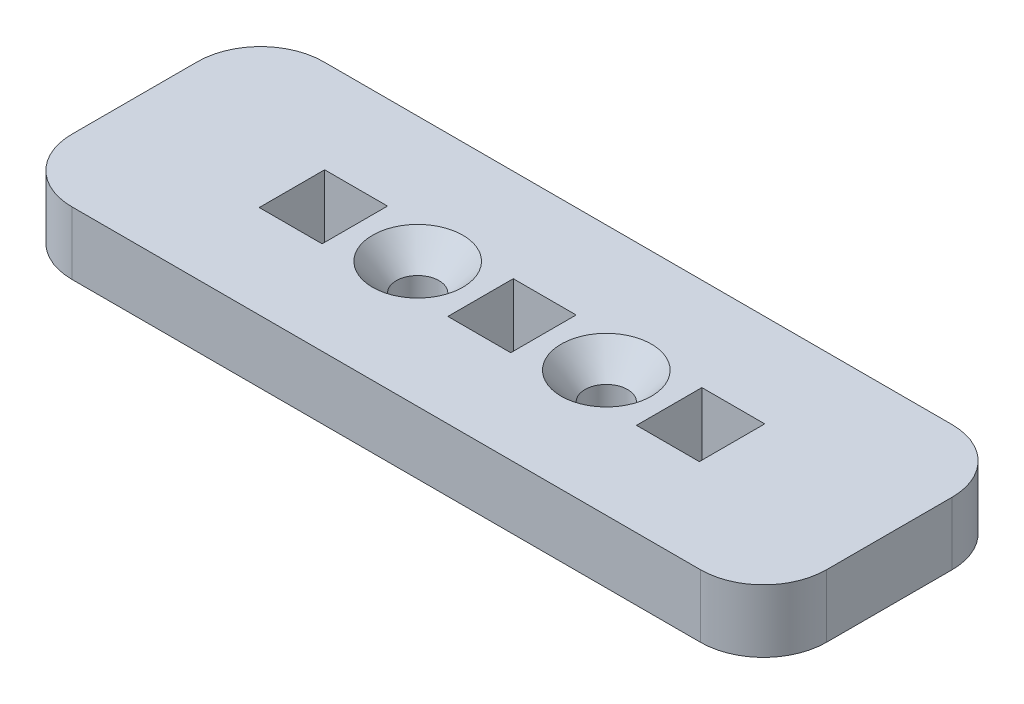
SolidWorks part; units mm, degrees
material "Acrylic (Medium-high impact)"
ref_plane "Front Plane" through (0, 0, 0) normal (0, 0, 1) x (1, 0, 0)
ref_plane "Top Plane" through (0, 0, 0) normal (0, 1, 0) x (1, 0, 0)
ref_plane "Right Plane" through (0, 0, 0) normal (1, 0, 0) x (0, 0, -1)
sketch "Sketch1" plane through (0, 0, 0) normal (0, 1, 0) x (1, 0, 0)
  line L0 (-38.1, 12.7) -> (38.1, -12.7) construction
  line L1 (-38.1, 12.7) -> (38.1, 12.7)
  line L2 (-38.1, 12.7) -> (-38.1, -12.7)
  line L3 (-38.1, -12.7) -> (38.1, -12.7)
  line L4 (38.1, 12.7) -> (38.1, -12.7)
  dimension "D1" = 76.2
  dimension "D2" = 25.4
extrude "Boss-Extrude1" add sketch "Sketch1" along normal blind 6.35
sketch "Sketch2" plane through (0, 6.35, 0) normal (0, 1, 0) x (1, 0, 0)
  line L0 (-3.175, 3.302) -> (3.175, -3.302) construction
  line L1 (-38.1, 0) -> (38.1, 0) construction
  line L2 (-38.1, 12.7) -> (-38.1, -12.7) construction
  line L3 (38.1, -12.7) -> (38.1, 12.7) construction
  point P8 (0, 0)
  line B0 (-3.175, 3.302) -> (3.175, 3.302)
  line B1 (3.175, 3.302) -> (3.175, -3.302)
  line B2 (3.175, -3.302) -> (-3.175, -3.302)
  line B3 (-3.175, -3.302) -> (-3.175, 3.302)
  line B4 (-22.225, 3.302) -> (-15.875, 3.302)
  line B5 (-15.875, 3.302) -> (-15.875, -3.302)
  line B6 (-15.875, -3.302) -> (-22.225, -3.302)
  line B7 (-22.225, -3.302) -> (-22.225, 3.302)
  circle B8 centre (-9.525, 0) radius 2.1526
  line B9 (15.875, 3.302) -> (22.225, 3.302)
  line B10 (22.225, 3.302) -> (22.225, -3.302)
  line B11 (15.875, -3.302) -> (22.225, -3.302)
  line B12 (15.875, 3.302) -> (15.875, -3.302)
  circle B13 centre (9.525, 0) radius 2.1527
sketch_block_instance "BOLT_HOLE_2X-1"
sketch_block "BOLT_HOLE_2X" parameters "D1"=4.3053, "D2"=6.35, "D3"=6.35, "D4"=6.604
extrude "Cut-Extrude1" cut sketch "Sketch2" against normal through all
fillet "Fillet1" radius 6.35 4 edges at (-38.1, 3.175, 12.7) (38.1, 3.175, 12.7) (-38.1, 3.175, -12.7) (38.1, 3.175, -12.7)
hole_wizard "CSK for #8 Flat Head Socket Cap Screw1" positions "Sketch4" profile "Sketch3" countersink size "#8" standard "ANSI Inch" end condition through all
sketch "Sketch4" plane through (0, 6.35, 0) normal (0, 1, 0) x (1, 0, 0)
  point P0 (-9.525, 0)
  point P3 (9.525, 0)
sketch "Sketch3" plane through (-9.525, 6.35, 0) normal (1, 0, 0) x (0, 0, 1)
  line L0 (0, 0) -> (0, 6.35)
  line L1 (0, 6.35) -> (2.1526, 6.35)
  line L2 (2.1526, 6.35) -> (2.1526, 2.7685)
  line L3 (2.1526, 2.7685) -> (4.5593, 0)
  line L5 (4.5593, 0) -> (0, 0)
  line L6 (-2.1527, 2.7685) -> (-4.5593, 0) construction
  line L11 (0, -6.35) -> (0, 107.95) construction
  dimension "Thru Hole Dia." = 4.3053
  dimension "Thru Hole Depth" = 6.35
  dimension "Near C'Sink Dia." = 9.1186
  dimension "Near C'Sink Angle" = 82
